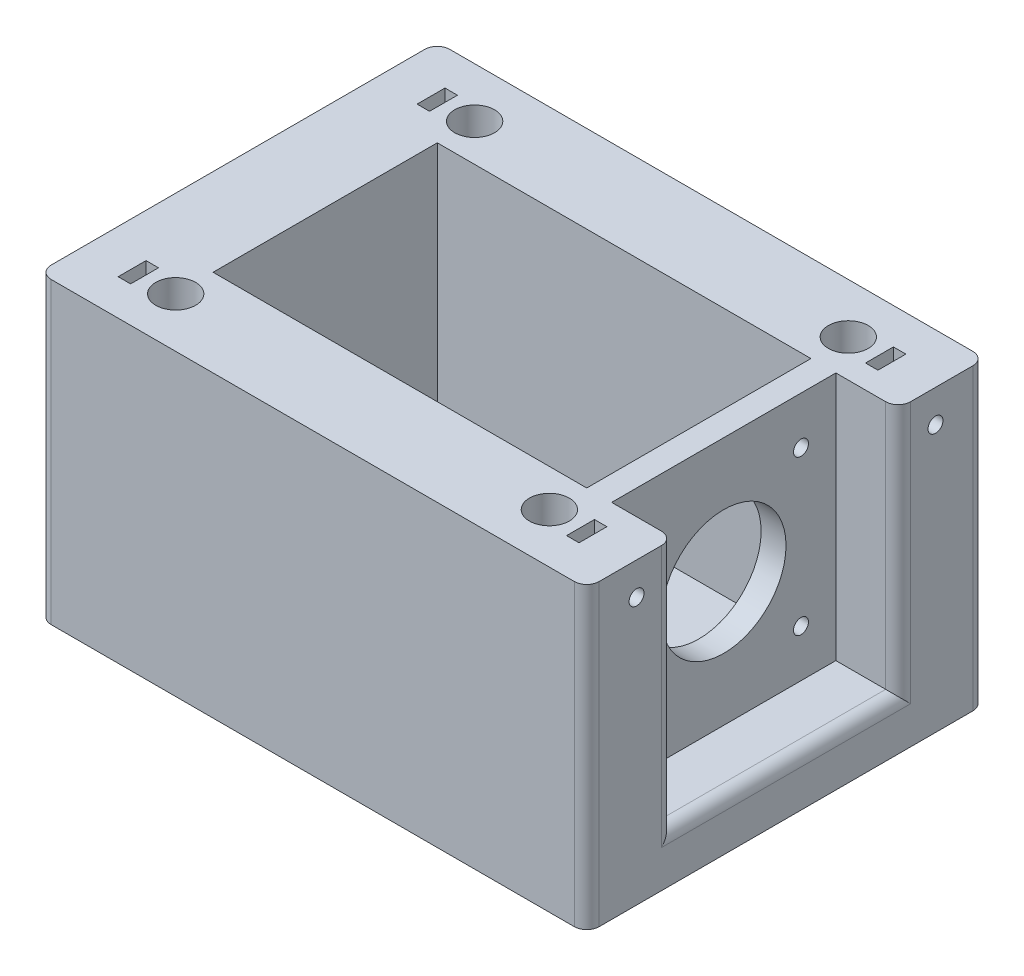
SolidWorks part; units mm, degrees
ref_plane "Front Plane" through (0, 0, 0) normal (0, 0, 1) x (1, 0, 0)
ref_plane "Top Plane" through (0, 0, 0) normal (0, 1, 0) x (1, 0, 0)
ref_plane "Right Plane" through (0, 0, 0) normal (1, 0, 0) x (0, 0, -1)
sketch "Sketch1" plane through (0, 0, 0) normal (0, 1, 0) x (1, 0, 0)
  line L1 (-55, 40) -> (55, 40)
  line L2 (-55, 40) -> (-55, -40)
  line L3 (-55, -40) -> (55, -40)
  line L4 (55, 40) -> (55, -40)
  line L5 (-55, 40) -> (55, -40) construction
  line L6 (-55, -40) -> (55, 40) construction
  point P0 (0, 0)
  dimension "D1" = 80
  dimension "D2" = 110
extrude "Boss-Extrude1" add sketch "Sketch1" along normal blind 60
sketch "Sketch2" plane through (0, 60, 0) normal (0, 1, 0) x (1, 0, 0)
  line L1 (-37.5, 22.5) -> (37.5, 22.5)
  line L2 (-37.5, 22.5) -> (-37.5, -22.5)
  line L3 (-37.5, -22.5) -> (37.5, -22.5)
  line L4 (37.5, 22.5) -> (37.5, -22.5)
  line L5 (-37.5, 22.5) -> (37.5, -22.5) construction
  line L6 (-37.5, -22.5) -> (37.5, 22.5) construction
  line L7 (-37.5, 30) -> (37.5, 30)
  line L8 (-37.5, 30) -> (-37.5, -30)
  line L9 (-37.5, -30) -> (37.5, -30)
  line L10 (37.5, 30) -> (37.5, -30)
  line L11 (-37.5, 30) -> (37.5, -30) construction
  line L12 (-37.5, -30) -> (37.5, 30) construction
  line L17 (55, -40) -> (55, 40) construction
  line L18 (42.5, 22.5) -> (55, 22.5)
  line L19 (42.5, 22.5) -> (42.5, -22.5)
  line L20 (42.5, -22.5) -> (55, -22.5)
  line L21 (55, 22.5) -> (55, -22.5)
  circle A0 centre (-37.5, 30) radius 4
  circle A1 centre (37.5, 30) radius 4
  circle A2 centre (37.5, -30) radius 4
  circle A3 centre (-37.5, -30) radius 4
  point P0 (0, 0)
  point P5 (0, 0)
  line M4 (55, -40) -> (55, 40)
  dimension "D5" = 8
  dimension "D1" = 45
  dimension "D2" = 75
  dimension "D3" = 60
  dimension "D4" = 75
  dimension "D8" = 5
  dimension "D9" = 45
  dimension "D10" = 0
  dimension "D11" = 0
  dimension "D12" = 12.5
  dimension "D6" = 2
  dimension "D7" = 2
extrude "Cut-Extrude2" cut sketch "Sketch2" against normal blind 50 contours L4 L1 L2 L3 | L7 A0 L8 | L8 A0 L7 | L10 A1 L7 | L7 A1 L10 | L8 A3 L9 | L9 A3 L8 | L9 A2 L10 | L10 A2 L9 | L19 L20 L18 M4
sketch "Sketch4" plane through (0, 60, 0) normal (0, 1, 0) x (1, 0, 0)
  line L1 (-45, 30) -> (45, 30)
  line L2 (-45, 30) -> (-45, -30)
  line L3 (-45, -30) -> (45, -30)
  line L4 (45, 30) -> (45, -30)
  line L5 (-45, 30) -> (45, -30) construction
  line L6 (-45, -30) -> (45, 30) construction
  line L7 (-46.25, 32.8) -> (-43.75, 32.8)
  line L8 (-46.25, 32.8) -> (-46.25, 27.2)
  line L9 (-46.25, 27.2) -> (-43.75, 27.2)
  line L10 (-43.75, 32.8) -> (-43.75, 27.2)
  line L11 (-46.25, 32.8) -> (-43.75, 27.2) construction
  line L12 (-46.25, 27.2) -> (-43.75, 32.8) construction
  line L20 (-46.25, -27.2) -> (-46.25, -32.8)
  line L21 (-46.25, -27.2) -> (-43.75, -27.2)
  line L22 (-43.75, -27.2) -> (-43.75, -32.8)
  line L23 (-46.25, -32.8) -> (-43.75, -32.8)
  line L24 (54.75, 32.8) -> (54.75, 27.2) [skipped]
  line L25 (54.75, 32.8) -> (57.25, 32.8) [skipped]
  line L26 (57.25, 32.8) -> (57.25, 27.2) [skipped]
  line L27 (54.75, 27.2) -> (57.25, 27.2) [skipped]
  line L28 (54.75, -27.2) -> (54.75, -32.8) [skipped]
  line L29 (54.75, -27.2) -> (57.25, -27.2) [skipped]
  line L30 (57.25, -27.2) -> (57.25, -32.8) [skipped]
  line L31 (54.75, -32.8) -> (57.25, -32.8) [skipped]
  line L32 (43.75, 32.8) -> (46.25, 32.8)
  line L33 (43.75, 32.8) -> (43.75, 27.2)
  line L34 (46.25, 32.8) -> (46.25, 27.2)
  line L35 (43.75, 27.2) -> (46.25, 27.2)
  line L36 (43.75, -27.2) -> (46.25, -27.2)
  line L37 (43.75, -27.2) -> (43.75, -32.8)
  line L38 (46.25, -27.2) -> (46.25, -32.8)
  line L39 (43.75, -32.8) -> (46.25, -32.8)
  point P0 (0, 0)
  point P5 (-45, 30)
  dimension "D1" = 2
  dimension "D2" = 5.6
  dimension "105" = 90
  dimension "D3" = 2.5
  dimension "D4" = 2
  dimension "D5" = 2
extrude "Cut-Extrude3" cut sketch "Sketch4" against normal blind 10 contours L10 L7 L8 L9 L2 L1 | L10 L1 L2 L9 | L20 L23 L22 L3 L2 L21 | L22 L21 L2 L3 | L36 L37 L3 L4 | L37 L39 L38 L36 L4 L3 | L4 L35 L34 L32 L33 L1 | L33 L35 L4 L1
sketch "Sketch5" plane through (55, 0, 0) normal (1, 0, 0) x (0, 0, -1)
  line L0 (-40, 60) -> (-22.5, 60) construction
  circle A0 centre (-30, 53.5) radius 1.5
  circle A1 centre (30, 53.5) radius 1.5
  dimension "D1" = 3
  dimension "D2" = 3
  dimension "D3" = 60
  dimension "D4" = 6.5
  dimension "D5" = 30
extrude "Cut-Extrude4" cut sketch "Sketch5" against normal blind 117
sketch "Sketch6" plane through (42.5, 0, 0) normal (1, 0, 0) x (0, 0, -1)
  line L1 (-15.5, 50.5) -> (15.5, 50.5)
  line L2 (-15.5, 50.5) -> (-15.5, 19.5)
  line L3 (-15.5, 19.5) -> (15.5, 19.5)
  line L4 (15.5, 50.5) -> (15.5, 19.5)
  line L5 (-15.5, 50.5) -> (15.5, 19.5) construction
  line L6 (-15.5, 19.5) -> (15.5, 50.5) construction
  line L7 (-22.5, 10) -> (22.5, 10) construction
  circle A0 centre (0, 35) radius 12.5
  circle A1 centre (-15.5, 50.5) radius 1.5
  circle A2 centre (15.5, 50.5) radius 1.5
  circle A3 centre (15.5, 19.5) radius 1.5
  circle A4 centre (-15.5, 19.5) radius 1.5
  point P0 (0, 35)
  point P15 (31, 35)
  point P18 (31, 4)
  point P21 (0, 4)
  dimension "D4" = 25
  dimension "D5" = 3
  dimension "D1" = 31
  dimension "D2" = 31
  dimension "D3" = 9.5
  dimension "D6" = 2
  dimension "D7" = 2
extrude "Cut-Extrude5" cut sketch "Sketch6" against normal blind 5 contours A0 | L1 A1 L2 | L2 A1 L1 | L1 A2 L4 | L4 A2 L1 | L3 A3 L4 | L4 A3 L3 | L3 A4 L2 | L2 A4 L3
fillet "Fillet1" radius 2.5 7 edges at (-55, 30, 40) (-55, 30, -40) (55, 30, -40) (55, 30, 40) (55, 35, -22.5) (55, 10, 0) (55, 35, 22.5)
